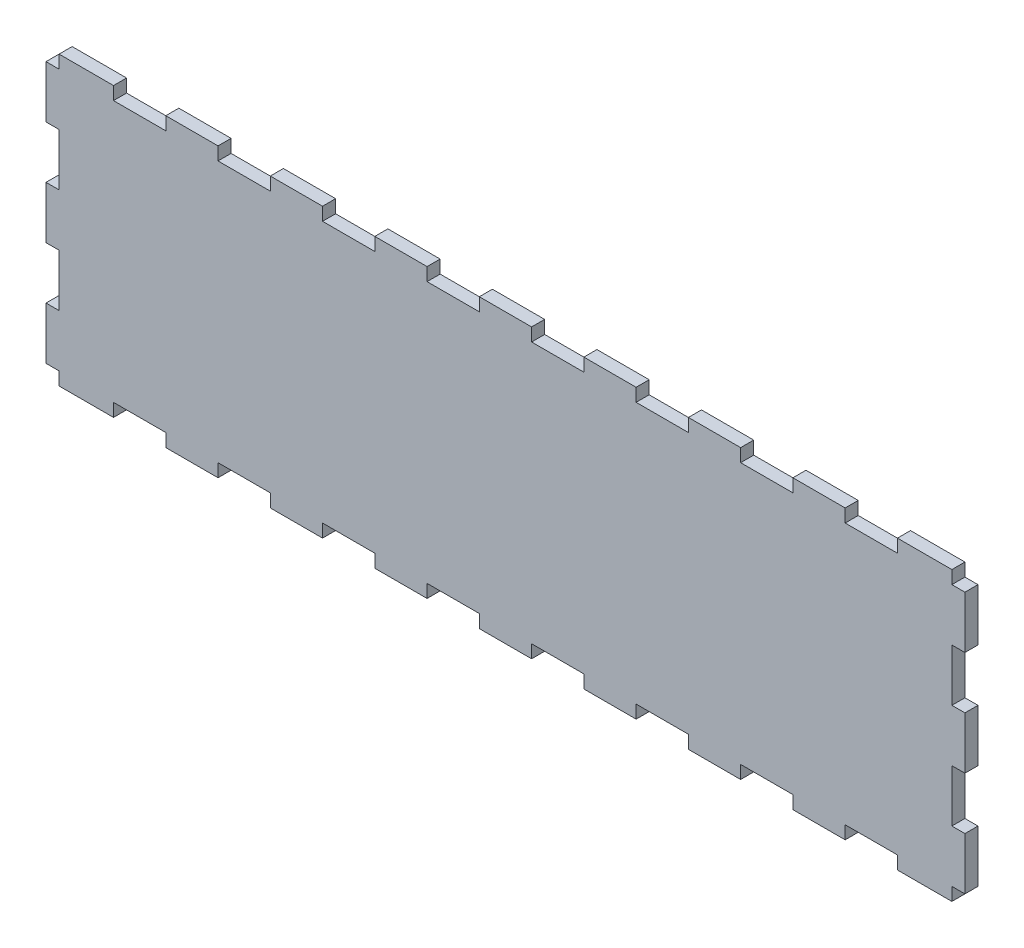
SolidWorks part; units mm, degrees
ref_plane "Front Plane" through (0, 0, 0) normal (0, 0, 1) x (1, 0, 0)
ref_plane "Top Plane" through (0, 0, 0) normal (0, 1, 0) x (1, 0, 0)
ref_plane "Right Plane" through (0, 0, 0) normal (1, 0, 0) x (0, 0, -1)
sketch "Sketch2" plane through (-276.446, 132.7357, 0) normal (0, 0, 1) x (1, 0, 0)
  line L0 (-78, 3) -> (-78, 0)
  line L1 (-78, 0) -> (-90, 0)
  line L2 (-90, 0) -> (-90, 3)
  line L3 (-90, 3) -> (-102.5, 3)
  line L5 (-78, 3) -> (-66, 3)
  line L6 (-66, 3) -> (-66, 0)
  line L7 (-66, 0) -> (-54, 0)
  line L8 (-54, 0) -> (-54, 3)
  line L9 (-54, 3) -> (-42, 3)
  line L10 (-42, 3) -> (-42, 0)
  line L11 (-42, 0) -> (-30, 0)
  line L12 (-30, 0) -> (-30, 3)
  line L13 (-30, 3) -> (-18, 3)
  line L14 (-18, 3) -> (-18, 0)
  line L15 (-18, 0) -> (-6, 0)
  line L18 (-6, 0) -> (-6, 3)
  line L19 (-6, 3) -> (6, 3)
  line L20 (6, 3) -> (6, 0)
  line L21 (6, 0) -> (18, 0)
  line L22 (18, 0) -> (18, 3)
  line L23 (18, 3) -> (30, 3)
  line L24 (30, 3) -> (30, 0)
  line L25 (30, 0) -> (42, 0)
  line L27 (42, 0) -> (42, 3)
  line L29 (42, 3) -> (54, 3)
  line L30 (54, 3) -> (54, 0)
  line L31 (54, 0) -> (66, 0)
  line L33 (66, 0) -> (66, 3)
  line L34 (66, 3) -> (78, 3)
  line L35 (78, 3) -> (78, 0)
  line L36 (78, 0) -> (90, 0)
  line L38 (90, 0) -> (90, 3)
  line L40 (90, 3) -> (102.5, 3)
  line L45 (-102.5, 3) -> (-102.5, -62.9994)
  line L47 (90, -62.9994) -> (102.5, -62.9994)
  line L48 (90, -59.9994) -> (90, -62.9994)
  line L49 (78, -59.9994) -> (90, -59.9994)
  line L50 (78, -62.9994) -> (78, -59.9994)
  line L51 (66, -62.9994) -> (78, -62.9994)
  line L52 (66, -59.9994) -> (66, -62.9994)
  line L53 (54, -59.9994) -> (66, -59.9994)
  line L54 (54, -62.9994) -> (54, -59.9994)
  line L55 (42, -62.9994) -> (54, -62.9994)
  line L56 (42, -59.9994) -> (42, -62.9994)
  line L57 (30, -59.9994) -> (42, -59.9994)
  line L58 (30, -62.9994) -> (30, -59.9994)
  line L59 (18, -62.9994) -> (30, -62.9994)
  line L60 (18, -59.9994) -> (18, -62.9994)
  line L61 (6, -59.9994) -> (18, -59.9994)
  line L62 (6, -62.9994) -> (6, -59.9994)
  line L63 (-6, -62.9994) -> (6, -62.9994)
  line L64 (-6, -59.9994) -> (-6, -62.9994)
  line L65 (-18, -59.9994) -> (-6, -59.9994)
  line L66 (-18, -62.9994) -> (-18, -59.9994)
  line L67 (-30, -62.9994) -> (-18, -62.9994)
  line L68 (-30, -59.9994) -> (-30, -62.9994)
  line L69 (-42, -59.9994) -> (-30, -59.9994)
  line L70 (-42, -62.9994) -> (-42, -59.9994)
  line L71 (-54, -62.9994) -> (-42, -62.9994)
  line L72 (-54, -59.9994) -> (-54, -62.9994)
  line L73 (-66, -59.9994) -> (-54, -59.9994)
  line L74 (-66, -62.9994) -> (-66, -59.9994)
  line L75 (-78, -62.9994) -> (-66, -62.9994)
  line L77 (-90, -62.9994) -> (-102.5, -62.9994)
  line L78 (-90, -59.9994) -> (-90, -62.9994)
  line L79 (-78, -59.9994) -> (-90, -59.9994)
  line L80 (-78, -62.9994) -> (-78, -59.9994)
  line L81 (102.5, 3) -> (102.5, -62.9994)
  dimension "D1" = 59.9994
  dimension "D2" = 12
  dimension "D3" = 3
  dimension "D4" = 12
extrude "Boss-Extrude1" add sketch "Sketch2" along normal blind 3
sketch "Sketch3" plane through (-276.446, 132.7357, 3) normal (0, 0, 1) x (1, 0, 0)
  line L1 (-102.5, 0) -> (-105.5, 0)
  line L2 (-102.5, 0) -> (-102.5, -12)
  line L3 (-102.5, -12) -> (-105.5, -12)
  line L4 (-105.5, 0) -> (-105.5, -12)
  line L5 (-90, 3) -> (-102.5, 3) construction
  line L6 (105.5, 0) -> (105.5, -12)
  line L7 (105.5, 0) -> (102.5, 0)
  line L8 (102.5, 0) -> (102.5, -12)
  line L9 (105.5, -12) -> (102.5, -12)
  line L10 (105.5, -24) -> (105.5, -36)
  line L11 (105.5, -24) -> (102.5, -24)
  line L12 (102.5, -24) -> (102.5, -36)
  line L13 (105.5, -36) -> (102.5, -36)
  line L14 (105.5, -48) -> (105.5, -60)
  line L15 (105.5, -48) -> (102.5, -48)
  line L16 (102.5, -48) -> (102.5, -60)
  line L17 (105.5, -60) -> (102.5, -60)
  line L18 (-102.5, -24) -> (-102.5, -36)
  line L19 (-102.5, -24) -> (-105.5, -24)
  line L20 (-105.5, -24) -> (-105.5, -36)
  line L21 (-102.5, -36) -> (-105.5, -36)
  line L22 (-102.5, -48) -> (-102.5, -60)
  line L23 (-102.5, -48) -> (-105.5, -48)
  line L24 (-105.5, -48) -> (-105.5, -60)
  line L25 (-102.5, -60) -> (-105.5, -60)
  line L29 (-102.5, 3) -> (-102.5, -62.9994) construction
  line L30 (102.5, 3) -> (102.5, -62.9994) construction
  dimension "D1" = 12
  dimension "D2" = 3
  dimension "D3" = 3
  dimension "D6" = 12
  dimension "D4" = 2
  dimension "D5" = 3
extrude "Boss-Extrude2" add sketch "Sketch3" against normal blind 3
